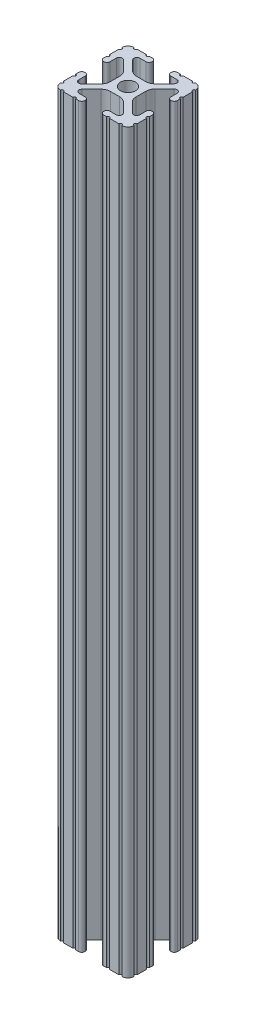
SolidWorks part; units mm, degrees
material "6061-T6 (SS)"
ref_plane "Front Plane" through (0, 0, 0) normal (0, 0, 1) x (1, 0, 0)
ref_plane "Top Plane" through (0, 0, 0) normal (0, 1, 0) x (1, 0, 0)
ref_plane "Right Plane" through (0, 0, 0) normal (1, 0, 0) x (0, 0, -1)
sketch "Sketch1" plane through (0, 0, 0) normal (0, 1, 0) x (0, 0, -1)
  line L0 (6.3331, -12.7) -> (9.5504, -12.7)
  line L1 (12.7, -9.5504) -> (12.7, -6.3331)
  line L2 (12.7, -5.3171) -> (12.7, -4.2875)
  line L3 (11.651, -3.2385) -> (11.5392, -3.2385)
  line L4 (10.4902, -4.2875) -> (10.4902, -6.4021)
  line L5 (8.7371, -7.1294) -> (5.441, -3.8408)
  line L6 (4.5085, -1.5932) -> (4.5085, 1.5932)
  line L7 (5.441, 3.8408) -> (8.7371, 7.1294)
  line L8 (10.4902, 6.4021) -> (10.4902, 4.2875)
  line L9 (11.5392, 3.2385) -> (11.651, 3.2385)
  line L10 (12.7, 4.2875) -> (12.7, 5.3171)
  line L11 (12.7, 6.3331) -> (12.7, 9.5504)
  line L12 (9.5504, 12.7) -> (6.3331, 12.7)
  line L13 (5.3171, 12.7) -> (4.2875, 12.7)
  line L14 (3.2385, 11.651) -> (3.2385, 11.5392)
  line L15 (4.2875, 10.4902) -> (6.4768, 10.4902)
  line L16 (7.207, 8.7244) -> (3.8983, 5.4232)
  line L17 (1.6558, 4.4958) -> (-1.6558, 4.4958)
  line L18 (-3.8983, 5.4232) -> (-7.207, 8.7244)
  line L19 (-6.4768, 10.4902) -> (-4.2875, 10.4902)
  line L20 (-3.2385, 11.5392) -> (-3.2385, 11.651)
  line L21 (-4.2875, 12.7) -> (-5.3171, 12.7)
  line L22 (-6.3331, 12.7) -> (-9.5504, 12.7)
  line L23 (-12.7, 9.5504) -> (-12.7, 6.3331)
  line L24 (-12.7, 5.3171) -> (-12.7, 4.2875)
  line L25 (-11.651, 3.2385) -> (-11.5392, 3.2385)
  line L26 (-10.4902, 4.2875) -> (-10.4902, 6.4021)
  line L27 (-8.7371, 7.1294) -> (-5.441, 3.8408)
  line L28 (-4.5085, 1.5932) -> (-4.5085, -1.5932)
  line L29 (-5.441, -3.8408) -> (-8.7371, -7.1294)
  line L30 (-10.4902, -6.4021) -> (-10.4902, -4.2875)
  line L31 (-11.5392, -3.2385) -> (-11.651, -3.2385)
  line L32 (-12.7, -4.2875) -> (-12.7, -5.3171)
  line L33 (-12.7, -6.3331) -> (-12.7, -9.5504)
  line L34 (-9.5504, -12.7) -> (-6.3331, -12.7)
  line L35 (-5.3171, -12.7) -> (-4.2875, -12.7)
  line L36 (-3.2385, -11.651) -> (-3.2385, -11.5392)
  line L37 (-4.2875, -10.4902) -> (-6.4164, -10.4902)
  line L38 (-7.1797, -8.6452) -> (-3.9523, -5.4237)
  line L39 (-1.7093, -4.4958) -> (1.7093, -4.4958)
  line L40 (3.9523, -5.4237) -> (7.1797, -8.6452)
  line L41 (6.4164, -10.4902) -> (4.2875, -10.4902)
  line L42 (3.2385, -11.5392) -> (3.2385, -11.651)
  line L43 (4.2875, -12.7) -> (5.3171, -12.7)
  circle A0 centre (0, 0) radius 2.6035
  arc A1 (6.3331, -12.7) -> (5.3171, -12.7) centre (5.8251, -12.7) ccw
  arc A2 (10.5664, -12.6998) -> (9.5504, -12.7) centre (10.0584, -12.7) ccw
  arc A3 (10.5664, -12.6998) -> (12.6998, -10.5664) centre (10.5918, -10.5918) ccw
  arc A4 (12.7, -9.5504) -> (12.6998, -10.5664) centre (12.7, -10.0584) ccw
  arc A5 (12.7, -5.3171) -> (12.7, -6.3331) centre (12.7, -5.8251) ccw
  arc A6 (12.7, -4.2875) -> (11.651, -3.2385) centre (11.651, -4.2875) ccw
  arc A7 (11.5392, -3.2385) -> (10.4902, -4.2875) centre (11.5392, -4.2875) ccw
  arc A8 (8.7371, -7.1294) -> (10.4902, -6.4021) centre (9.4628, -6.4021) ccw
  arc A9 (5.441, 3.8408) -> (4.5085, 1.5932) centre (7.6835, 1.5932) ccw
  arc A10 (10.4902, 6.4021) -> (8.7371, 7.1294) centre (9.4628, 6.4021) ccw
  arc A11 (10.4902, 4.2875) -> (11.5392, 3.2385) centre (11.5392, 4.2875) ccw
  arc A12 (11.651, 3.2385) -> (12.7, 4.2875) centre (11.651, 4.2875) ccw
  arc A13 (12.7, 6.3331) -> (12.7, 5.3171) centre (12.7, 5.8251) ccw
  arc A14 (12.6998, 10.5664) -> (12.7, 9.5504) centre (12.7, 10.0584) ccw
  arc A15 (12.6998, 10.5664) -> (10.5664, 12.6998) centre (10.5918, 10.5918) ccw
  arc A16 (9.5504, 12.7) -> (10.5664, 12.6998) centre (10.0584, 12.7) ccw
  arc A17 (5.3171, 12.7) -> (6.3331, 12.7) centre (5.8251, 12.7) ccw
  arc A18 (4.2875, 12.7) -> (3.2385, 11.651) centre (4.2875, 11.651) ccw
  arc A19 (3.2385, 11.5392) -> (4.2875, 10.4902) centre (4.2875, 11.5392) ccw
  arc A20 (7.207, 8.7244) -> (6.4768, 10.4902) centre (6.4768, 9.4563) ccw
  arc A21 (1.6558, 4.4958) -> (3.8983, 5.4232) centre (1.6558, 7.6708) ccw
  arc A22 (-3.8983, 5.4232) -> (-1.6558, 4.4958) centre (-1.6558, 7.6708) ccw
  arc A23 (-6.4768, 10.4902) -> (-7.207, 8.7244) centre (-6.4768, 9.4563) ccw
  arc A24 (-4.2875, 10.4902) -> (-3.2385, 11.5392) centre (-4.2875, 11.5392) ccw
  arc A25 (-3.2385, 11.651) -> (-4.2875, 12.7) centre (-4.2875, 11.651) ccw
  arc A26 (-6.3331, 12.7) -> (-5.3171, 12.7) centre (-5.8251, 12.7) ccw
  arc A27 (-10.5664, 12.6998) -> (-9.5504, 12.7) centre (-10.0584, 12.7) ccw
  arc A28 (-10.5664, 12.6998) -> (-12.6998, 10.5664) centre (-10.5918, 10.5918) ccw
  arc A29 (-12.7, 9.5504) -> (-12.6998, 10.5664) centre (-12.7, 10.0584) ccw
  arc A30 (-12.7, 5.3171) -> (-12.7, 6.3331) centre (-12.7, 5.8251) ccw
  arc A31 (-12.7, 4.2875) -> (-11.651, 3.2385) centre (-11.651, 4.2875) ccw
  arc A32 (-11.5392, 3.2385) -> (-10.4902, 4.2875) centre (-11.5392, 4.2875) ccw
  arc A33 (-8.7371, 7.1294) -> (-10.4902, 6.4021) centre (-9.4628, 6.4021) ccw
  arc A34 (-4.5085, 1.5932) -> (-5.441, 3.8408) centre (-7.6835, 1.5932) ccw
  arc A35 (-5.441, -3.8408) -> (-4.5085, -1.5932) centre (-7.6835, -1.5932) ccw
  arc A36 (-10.4902, -6.4021) -> (-8.7371, -7.1294) centre (-9.4628, -6.4021) ccw
  arc A37 (-10.4902, -4.2875) -> (-11.5392, -3.2385) centre (-11.5392, -4.2875) ccw
  arc A38 (-11.651, -3.2385) -> (-12.7, -4.2875) centre (-11.651, -4.2875) ccw
  arc A39 (-12.7, -6.3331) -> (-12.7, -5.3171) centre (-12.7, -5.8251) ccw
  arc A40 (-12.6998, -10.5664) -> (-12.7, -9.5504) centre (-12.7, -10.0584) ccw
  arc A41 (-12.6998, -10.5664) -> (-10.5664, -12.6998) centre (-10.5918, -10.5918) ccw
  arc A42 (-9.5504, -12.7) -> (-10.5664, -12.6998) centre (-10.0584, -12.7) ccw
  arc A43 (-5.3171, -12.7) -> (-6.3331, -12.7) centre (-5.8251, -12.7) ccw
  arc A44 (-4.2875, -12.7) -> (-3.2385, -11.651) centre (-4.2875, -11.651) ccw
  arc A45 (-3.2385, -11.5392) -> (-4.2875, -10.4902) centre (-4.2875, -11.5392) ccw
  arc A46 (-7.1797, -8.6452) -> (-6.4164, -10.4902) centre (-6.4164, -9.4098) ccw
  arc A47 (-1.7093, -4.4958) -> (-3.9523, -5.4237) centre (-1.7093, -7.6708) ccw
  arc A48 (3.9523, -5.4237) -> (1.7093, -4.4958) centre (1.7093, -7.6708) ccw
  arc A49 (6.4164, -10.4902) -> (7.1797, -8.6452) centre (6.4164, -9.4098) ccw
  arc A50 (4.2875, -10.4902) -> (3.2385, -11.5392) centre (4.2875, -11.5392) ccw
  arc A51 (3.2385, -11.651) -> (4.2875, -12.7) centre (4.2875, -11.651) ccw
  arc A52 (5.441, -3.8408) -> (4.5085, -1.5932) centre (7.6835, -1.5932) cw
  dimension "D1" = 3.175
extrude "Boss-Extrude1" add sketch "Sketch1" along normal mid plane 254
